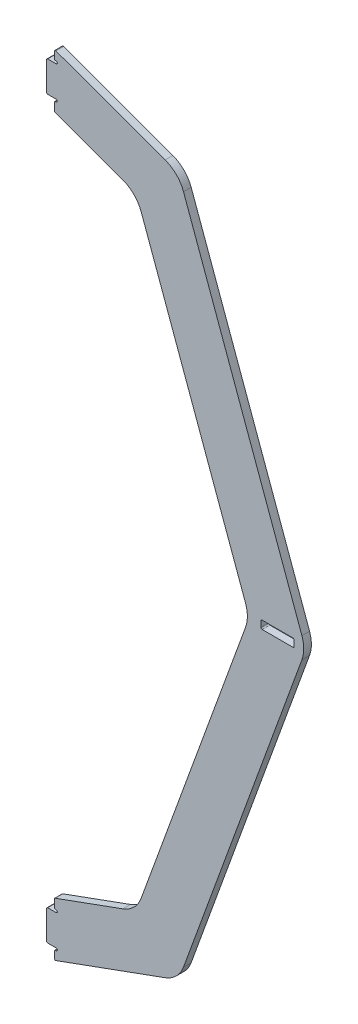
SolidWorks part; units mm, degrees
material "6061-T6 (SS)"
ref_plane "Front Plane" through (0, 0, 0) normal (0, 0, 1) x (1, 0, 0)
ref_plane "Top Plane" through (0, 0, 0) normal (0, 1, 0) x (1, 0, 0)
ref_plane "Right Plane" through (0, 0, 0) normal (1, 0, 0) x (0, 0, -1)
sketch "Sketch1" plane through (0, 0, 0) normal (0, 0, 1) x (1, 0, 0)
  line L0 (114.3, 158.75) -> (114.3, 146.05)
  line L1 (114.3, 146.05) -> (117.475, 146.05)
  line L2 (114.3, 158.75) -> (117.475, 158.75)
  line L3 (117.475, 158.75) -> (117.475, 163.576)
  line L4 (117.475, 146.05) -> (117.475, 141.224)
  line L5 (117.475, 141.224) -> (151.4771, 128.8483)
  line L6 (151.4771, 128.8483) -> (198.374, 0)
  line L7 (117.475, 163.576) -> (169.0357, 144.8095)
  line L8 (169.0357, 144.8095) -> (221.742, 0)
  line L9 (169.0357, -144.8095) -> (221.742, 0)
  line L10 (117.475, -163.576) -> (169.0357, -144.8095)
  line L11 (151.4771, -128.8483) -> (198.374, 0)
  line L12 (117.475, -141.224) -> (151.4771, -128.8483)
  line L13 (55, 0) -> (-55, 0) construction
  line L16 (117.475, -146.05) -> (117.475, -141.224)
  line L17 (117.475, -158.75) -> (117.475, -163.576)
  line L18 (114.3, -158.75) -> (117.475, -158.75)
  line L19 (114.3, -146.05) -> (117.475, -146.05)
  line L20 (114.3, -158.75) -> (114.3, -146.05)
  line L34 (216.916, -1.6764) -> (203.2, -1.6764)
  line L35 (216.916, -1.6764) -> (216.916, 1.6764)
  line L36 (216.916, 1.6764) -> (203.2, 1.6764)
  line L37 (203.2, -1.6764) -> (203.2, 1.6764)
  line L38 (216.916, -1.6764) -> (203.2, 1.6764) construction
  line L39 (216.916, 1.6764) -> (203.2, -1.6764) construction
  point P2 (114.3, 152.4)
  point P22 (210.058, 0)
  dimension "D1" = 114.3
  dimension "D2" = 3.175
  dimension "D3" = 12.7
  dimension "D4" = 152.4
  dimension "D5" = 4.826
  dimension "D6" = 20
  dimension "D7" = 20
  dimension "D8" = 4.826
  dimension "D10" = 4.826
  dimension "D15" = 3.3528
  dimension "D16" = 13.716
  dimension "D17" = 203.2
extrude "Boss-Extrude1" add sketch "Sketch1" along normal blind 3.175
fillet "Fillet1" radius 12.7 6 edges at (151.4771, -128.8483, 1.5875) (169.0357, -144.8095, 1.5875) (221.742, 0, 1.5875) (198.374, 0, 1.5875) (169.0357, 144.8095, 1.5875) (151.4771, 128.8483, 1.5875)
sketch "Sketch2" plane through (0, 0, 3.175) normal (0, 0, 1) x (1, 0, 0)
  line L0 (117.475, 146.05) -> (118.237, 146.05)
  line L1 (118.237, 145.034) -> (117.475, 145.034)
  line L2 (117.475, 146.05) -> (117.475, 141.224) construction
  line L3 (117.475, 158.75) -> (118.237, 158.75)
  line L4 (118.237, 159.766) -> (117.475, 159.766)
  line L5 (117.475, 163.576) -> (117.475, 158.75) construction
  line L6 (117.475, 158.75) -> (117.475, 159.766)
  line L7 (117.475, 145.034) -> (117.475, 146.05)
  line L8 (1.7463, 0) -> (-1.7463, 0) construction
  line L9 (117.475, -145.034) -> (117.475, -146.05)
  line L10 (117.475, -158.75) -> (117.475, -159.766)
  line L11 (118.237, -159.766) -> (117.475, -159.766)
  line L12 (117.475, -158.75) -> (118.237, -158.75)
  line L13 (118.237, -145.034) -> (117.475, -145.034)
  line L14 (117.475, -146.05) -> (118.237, -146.05)
  arc A0 (118.237, 146.05) -> (118.237, 145.034) centre (118.237, 145.542) cw
  arc A1 (118.237, 158.75) -> (118.237, 159.766) centre (118.237, 159.258) ccw
  arc A2 (118.237, -158.75) -> (118.237, -159.766) centre (118.237, -159.258) cw
  arc A3 (118.237, -146.05) -> (118.237, -145.034) centre (118.237, -145.542) ccw
  dimension "D2" = 0.508
  dimension "D1" = 0.762
extrude "Cut-Extrude1" cut sketch "Sketch2" against normal through all
fillet "Fillet2" radius 0.508 16 edges at (117.475, -141.224, 1.5875) (117.475, -145.034, 1.5875) (114.3, -146.05, 1.5875) (114.3, -158.75, 1.5875) (117.475, -159.766, 1.5875) (117.475, -163.576, 1.5875) (216.916, -1.6764, 1.5875) (216.916, 1.6764, 1.5875) (203.2, 1.6764, 1.5875) (203.2, -1.6764, 1.5875) (117.475, 141.224, 1.5875) (117.475, 145.034, 1.5875) (114.3, 146.05, 1.5875) (114.3, 158.75, 1.5875) (117.475, 159.766, 1.5875) (117.475, 163.576, 1.5875)
